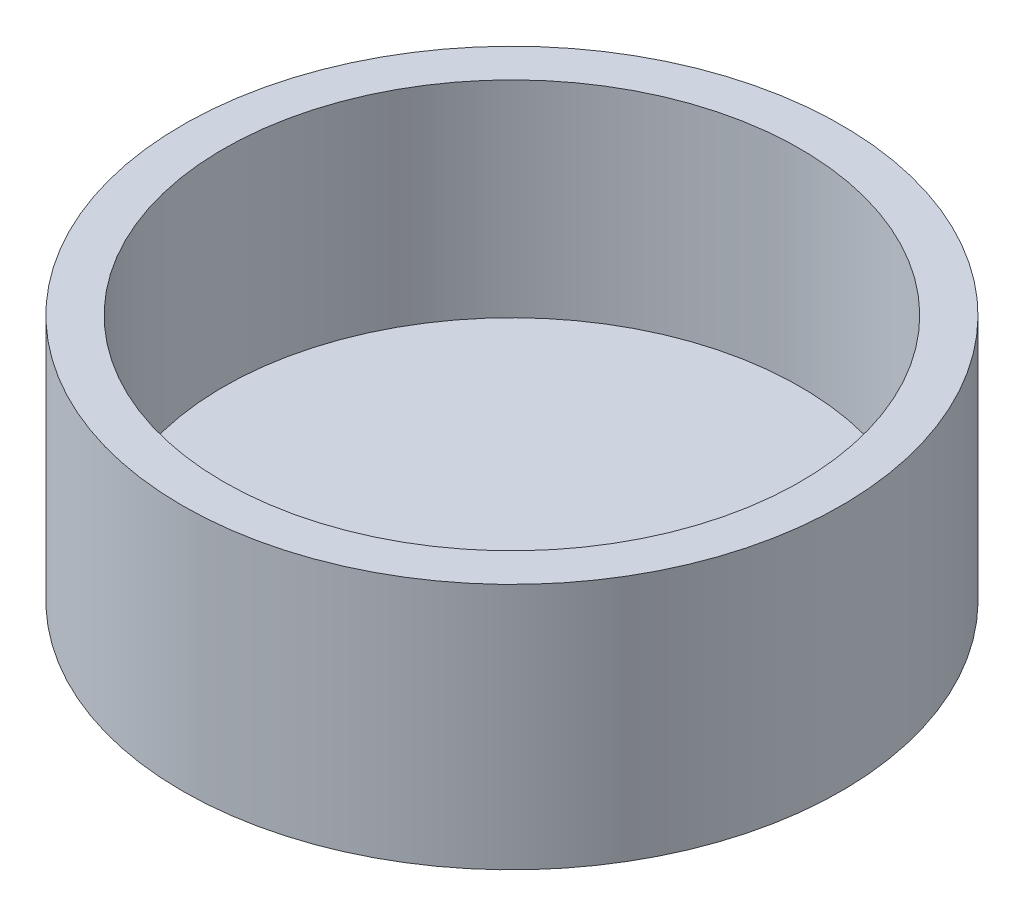
SolidWorks part; units mm, degrees
material "AISI 1020"
ref_plane "Front Plane" through (0, 0, 0) normal (0, 0, 1) x (1, 0, 0)
ref_plane "Top Plane" through (0, 0, 0) normal (0, 1, 0) x (1, 0, 0)
ref_plane "Right Plane" through (0, 0, 0) normal (1, 0, 0) x (0, 0, -1)
sketch "Sketch1" plane through (0, 0, 0) normal (0, 1, 0) x (1, 0, 0)
  circle A0 centre (0, 0) radius 101.6
  dimension "D1" = 203.2
extrude "Boss-Extrude1" add sketch "Sketch1" along normal blind 76.2
sketch "Sketch2" plane through (0, 76.2, 0) normal (0, 1, 0) x (1, 0, 0)
  circle A0 centre (0, 0) radius 88.9
  circle A1 centre (0, 0) radius 101.6 construction
  dimension "D1" = 12.7
extrude "Cut-Extrude1" cut sketch "Sketch2" against normal blind 63.5
sketch "Sketch3" plane through (0, 0, 0) normal (0, -1, 0) x (1, 0, 0)
  circle A0 centre (0, 0) radius 12.7
  circle A1 centre (0, 0) radius 9.525
  dimension "D1" = 25.4
  dimension "D2" = 19.05
extrude "Boss-Extrude2" add sketch "Sketch3" along normal blind 25.4
